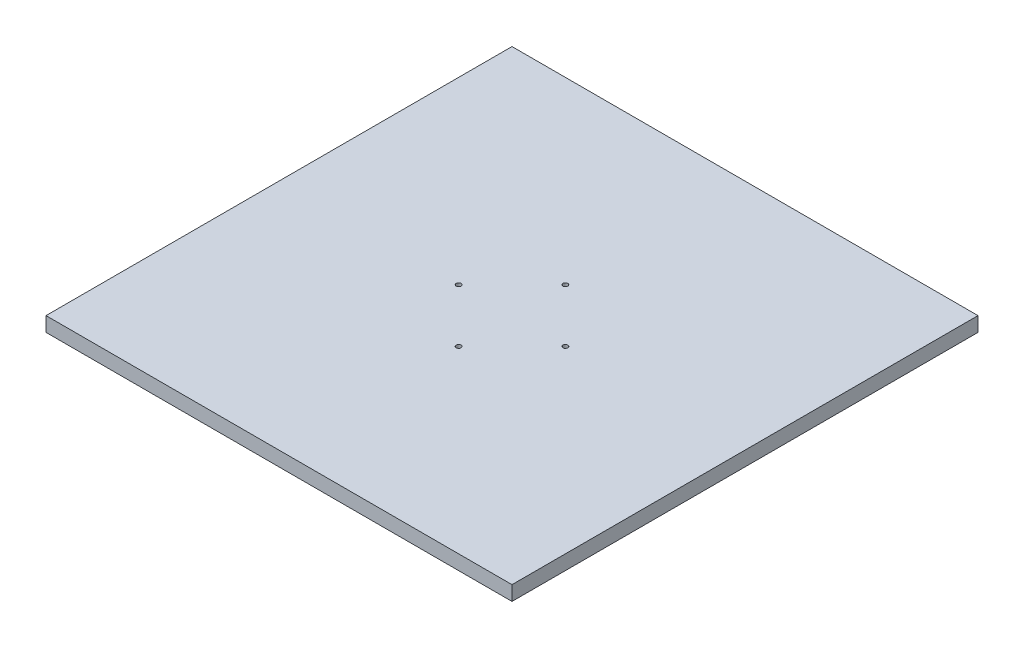
SolidWorks part; units mm, degrees
material "Maple"
ref_plane "Front Plane" through (0, 0, 0) normal (0, 0, 1) x (1, 0, 0)
ref_plane "Top Plane" through (0, 0, 0) normal (0, 1, 0) x (1, 0, 0)
ref_plane "Right Plane" through (0, 0, 0) normal (1, 0, 0) x (0, 0, -1)
sketch "Sketch1" plane through (0, 0, 0) normal (0, 1, 0) x (1, 0, 0)
  line L1 (0, 0) -> (609.6, 0)
  line L2 (0, 0) -> (0, 609.6)
  line L3 (0, 609.6) -> (609.6, 609.6)
  line L4 (609.6, 0) -> (609.6, 609.6)
  dimension "D1" = 609.6
  dimension "D2" = 609.6
extrude "Boss-Extrude1" add sketch "Sketch1" along normal blind 19.05
sketch "Sketch2" plane through (0, 19.05, 0) normal (0, 1, 0) x (1, 0, 0)
  line L0 (304.8, 609.6) -> (304.8, 0) construction
  line L1 (609.6, 609.6) -> (0, 609.6) construction
  line L2 (0, 0) -> (609.6, 0) construction
  line L3 (0, 304.8) -> (609.6, 304.8) construction
  line L4 (0, 609.6) -> (0, 0) construction
  line L5 (609.6, 0) -> (609.6, 609.6) construction
  circle A0 centre (304.8, 304.8) radius 69.85 construction
  circle A1 centre (304.8, 374.65) radius 3.175
  circle A2 centre (234.95, 304.8) radius 3.175
  circle A3 centre (374.65, 304.8) radius 3.175
  circle A4 centre (304.8, 234.95) radius 3.175
  point P16 (234.95, 304.8)
  dimension "D1" = 139.7
  dimension "D2" = 6.35
  dimension "D3" = 6.35
  dimension "D4" = 6.35
  dimension "D5" = 6.35
extrude "Cut-Extrude1" cut sketch "Sketch2" against normal through all
sketch "Sketch3" plane through (0, 0, 0) normal (0, 1, 0) x (1, 0, 0)
  line L0 (609.6, 304.8) -> (-49390.4, 304.8) construction
  line L1 (609.6, 0) -> (609.6, 609.6) construction
  line L2 (304.8, 0) -> (304.8, 50000) construction
  line L3 (0, 0) -> (609.6, 0) construction
  circle A0 centre (304.8, 304.8) radius 8.7658
  point P4 (609.6, 304.8)
  point P9 (304.8, 0)
  point P10 (304.8, 304.8)
extrude "Cut-Extrude2" cut sketch "Sketch3" along normal blind 2.54
hole_wizard "Hole1" positions "Sketch4" profile "Sketch5" legacy
sketch "Sketch4" plane through (0, 0, 0) normal (0, -1, 0) x (-1, 0, 0)
  point P0 (-234.95, 304.8)
  point P3 (-304.8, 234.95)
  point P6 (-374.65, 304.8)
  point P9 (-304.8, 374.65)
sketch "Sketch5" plane through (234.95, 0, -304.8) normal (1, 0, 0) x (0, 0, -1)
  line L0 (0, 0) -> (0, 25.4)
  line L1 (0, 25.4) -> (3.175, 25.4)
  line L2 (3.175, 25.4) -> (3.175, 6.35)
  line L3 (3.175, 6.35) -> (9.525, 6.35)
  line L4 (9.525, 6.35) -> (9.525, 0)
  line L5 (9.525, 0) -> (0, 0)
  line L6 (0, 110) -> (0, -10) construction
  dimension "Diameter" = 6.35
  dimension "Depth" = 25.4
  dimension "C-Bore Diameter" = 19.05
  dimension "C-Bore Depth" = 6.35
